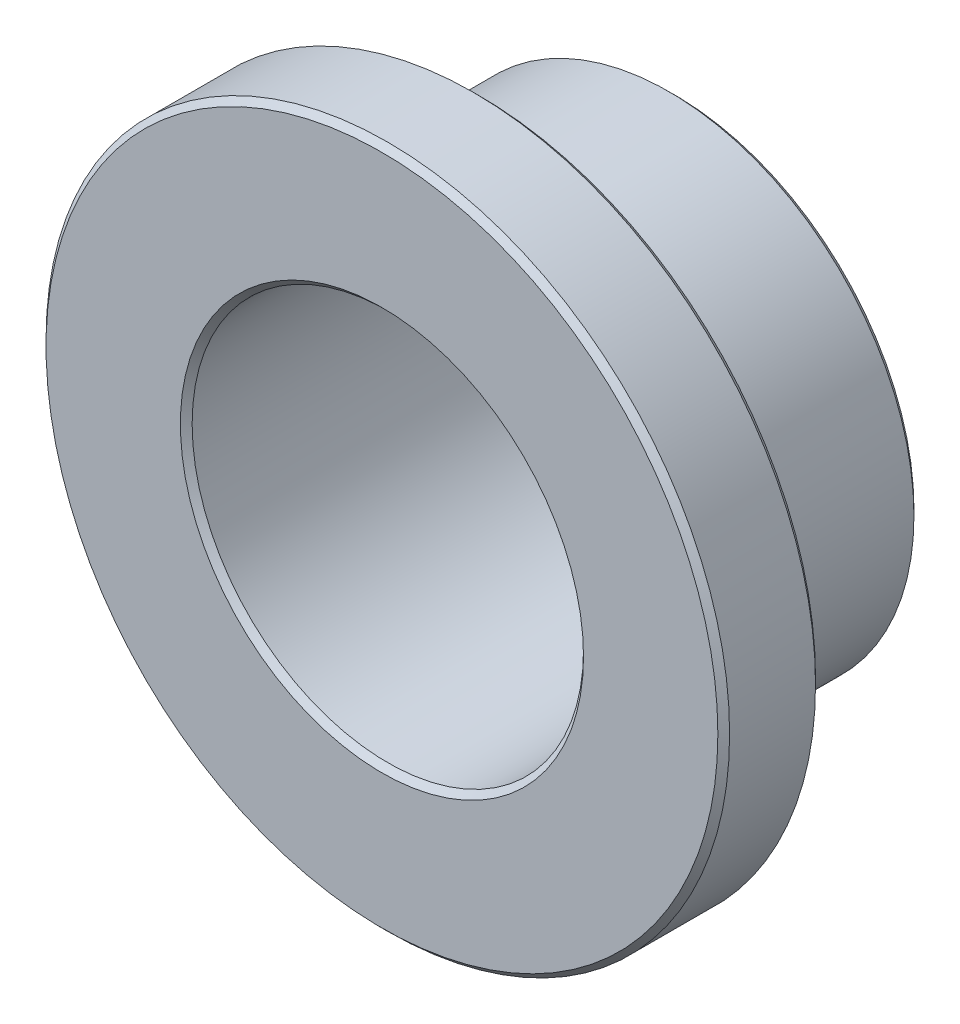
SolidWorks part; units mm, degrees
material "SAE 841 Sintered Bronze"
ref_plane "Front" through (0, 0, 0) normal (0, 0, 1) x (1, 0, 0)
ref_plane "Top" through (0, 0, 0) normal (0, 1, 0) x (1, 0, 0)
ref_plane "Right" through (0, 0, 0) normal (1, 0, 0) x (0, 0, -1)
sketch "Sketch1" plane through (0, 0, 0) normal (0, 0, 1) x (1, 0, 0)
  circle A0 centre (0, 0) radius 6.3627
  circle A1 centre (0, 0) radius 7.9629
  circle A2 centre (0, 0) radius 11.1125
  dimension "ID" = 12.7254
  dimension "OD" = 15.9258
  dimension "Flange OD" = 22.225
sketch "Sketch2" plane through (0, 0, 0) normal (1, 0, 0) x (0, 0, -1)
  line L0 (-4.7625, -11.1125) -> (4.7625, -11.1125) construction
  line L1 (0, 11.1125) -> (0, -11.1125) construction
  line L3 (-1.5875, 7.9629) -> (4.7625, 7.9629) construction
  point P3 (0, -11.1125)
  point P7 (0, 7.9629)
  point P9 (-1.5875, -11.1125)
  point P10 (-4.7625, 11.1125)
  point P23 (0, 11.1125)
  dimension "Flange Thickness" = 3.175
  dimension "Length" = 9.525
sketch "Sketch3" plane through (0, 0, 0) normal (0, 0, 1) x (1, 0, 0)
  circle A0 centre (0, 0) radius 11.1125 construction
  circle A1 centre (0, 0) radius 11.1125
  circle A2 centre (0, 0) radius 6.3627 construction
  circle A3 centre (0, 0) radius 6.3627
extrude "Boss-Extrude1" add sketch "Sketch3" against normal up to vertex (-1.5875 mm away) from vertex at 4.7625 starting at point (0, -11.1125, 4.7625)
sketch "Sketch4" plane through (0, 0, 0) normal (0, 0, 1) x (1, 0, 0)
  circle A0 centre (0, 0) radius 6.3627 construction
  circle A1 centre (0, 0) radius 7.9629 construction
  circle A2 centre (0, 0) radius 6.3627
  circle A3 centre (0, 0) radius 7.9629
extrude "Boss-Extrude2" add sketch "Sketch4" against normal up to vertex (4.7625 mm away) from vertex at 1.5875 starting at point (0, -11.1125, 1.5875)
chamfer "Chamfer1" distance 0.1909 angle 45 6 edges at (6.3627, 0, 4.7625) (11.1125, 0, 4.7625) (11.1125, 0, 1.5875) (7.9629, 0, 1.5875) (6.3627, 0, -4.7625) (7.9629, 0, -4.7625)
equation "\"D1@Chamfer1\"=\"ID@Sketch1\"*0.015"
